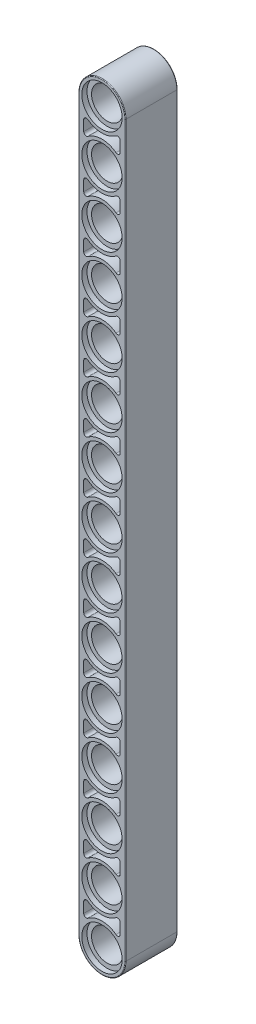
SolidWorks part; units mm, degrees
ref_plane "Front Plane" through (0, 0, 0) normal (0, 0, 1) x (1, 0, 0)
ref_plane "Top Plane" through (0, 0, 0) normal (0, 1, 0) x (1, 0, 0)
ref_plane "Right Plane" through (0, 0, 0) normal (1, 0, 0) x (0, 0, -1)
ref_plane "Plane1" through (0, 0, 4) normal (0, 0, 1) x (1, 0, 0)
sketch "Sketch1" plane through (0, 0, 4) normal (0, 0, 1) x (1, 0, 0)
  line L0 (3.6, -56) -> (3.6, 56)
  line L1 (-3.6, 56) -> (-3.6, -56)
  line L2 (3.6, 0) -> (-3.6, 0) construction
  arc A0 (3.6, 56) -> (-3.6, 56) centre (0, 56) ccw
  arc A1 (-3.6, -56) -> (3.6, -56) centre (0, -56) ccw
  point P6 (0, 0)
  dimension "D2" = 3.6
  dimension "D1" = 112
extrude "Boss-Extrude1" add sketch "Sketch1" against normal blind 8
sketch "Sketch2" plane through (0, 0, 4) normal (0, 0, 1) x (1, 0, 0)
  line L0 (-2.8, -27.2) -> (-2.8, -28.8)
  line L1 (2.8, -28.8) -> (2.8, -27.2)
  arc A0 (2.16, -26.88) -> (-2.16, -26.88) centre (0, -24) cw
  arc A1 (-2.16, -26.88) -> (-2.8, -27.2) centre (-2.4, -27.2) ccw
  arc A2 (-2.8, -28.8) -> (-2.16, -29.12) centre (-2.4, -28.8) ccw
  arc A3 (-2.16, -29.12) -> (2.16, -29.12) centre (0, -32) cw
  arc A4 (2.16, -29.12) -> (2.8, -28.8) centre (2.4, -28.8) ccw
  arc A5 (2.8, -27.2) -> (2.16, -26.88) centre (2.4, -27.2) ccw
extrude "Cut-Extrude1" cut sketch "Sketch2" against normal blind 3.1
sketch "Sketch3" plane through (0, 0, 4) normal (0, 0, 1) x (1, 0, 0)
  line L0 (-2.8, -11.2) -> (-2.8, -12.8)
  line L1 (2.8, -12.8) -> (2.8, -11.2)
  arc A0 (2.16, -10.88) -> (-2.16, -10.88) centre (0, -8) cw
  arc A1 (-2.16, -10.88) -> (-2.8, -11.2) centre (-2.4, -11.2) ccw
  arc A2 (-2.8, -12.8) -> (-2.16, -13.12) centre (-2.4, -12.8) ccw
  arc A3 (-2.16, -13.12) -> (2.16, -13.12) centre (0, -16) cw
  arc A4 (2.16, -13.12) -> (2.8, -12.8) centre (2.4, -12.8) ccw
  arc A5 (2.8, -11.2) -> (2.16, -10.88) centre (2.4, -11.2) ccw
extrude "Cut-Extrude2" cut sketch "Sketch3" against normal blind 3.1
sketch "Sketch4" plane through (0, 0, 4) normal (0, 0, 1) x (1, 0, 0)
  line L0 (-2.8, 4.8) -> (-2.8, 3.2)
  line L1 (2.8, 3.2) -> (2.8, 4.8)
  arc A0 (2.16, 5.12) -> (-2.16, 5.12) centre (0, 8) cw
  arc A1 (-2.16, 5.12) -> (-2.8, 4.8) centre (-2.4, 4.8) ccw
  arc A2 (-2.8, 3.2) -> (-2.16, 2.88) centre (-2.4, 3.2) ccw
  arc A3 (-2.16, 2.88) -> (2.16, 2.88) centre (0, 0) cw
  arc A4 (2.16, 2.88) -> (2.8, 3.2) centre (2.4, 3.2) ccw
  arc A5 (2.8, 4.8) -> (2.16, 5.12) centre (2.4, 4.8) ccw
extrude "Cut-Extrude3" cut sketch "Sketch4" against normal blind 3.1
sketch "Sketch5" plane through (0, 0, 4) normal (0, 0, 1) x (1, 0, 0)
  line L0 (-2.8, 20.8) -> (-2.8, 19.2)
  line L1 (2.8, 19.2) -> (2.8, 20.8)
  arc A0 (2.16, 21.12) -> (-2.16, 21.12) centre (0, 24) cw
  arc A1 (-2.16, 21.12) -> (-2.8, 20.8) centre (-2.4, 20.8) ccw
  arc A2 (-2.8, 19.2) -> (-2.16, 18.88) centre (-2.4, 19.2) ccw
  arc A3 (-2.16, 18.88) -> (2.16, 18.88) centre (0, 16) cw
  arc A4 (2.16, 18.88) -> (2.8, 19.2) centre (2.4, 19.2) ccw
  arc A5 (2.8, 20.8) -> (2.16, 21.12) centre (2.4, 20.8) ccw
extrude "Cut-Extrude4" cut sketch "Sketch5" against normal blind 3.1
sketch "Sketch6" plane through (0, 0, 4) normal (0, 0, 1) x (1, 0, 0)
  line L0 (2.8, 27.2) -> (2.8, 28.8)
  line L1 (-2.8, 28.8) -> (-2.8, 27.2)
  arc A0 (2.8, 28.8) -> (2.16, 29.12) centre (2.4, 28.8) ccw
  arc A1 (2.16, 29.12) -> (-2.16, 29.12) centre (0, 32) cw
  arc A2 (-2.16, 29.12) -> (-2.8, 28.8) centre (-2.4, 28.8) ccw
  arc A3 (-2.8, 27.2) -> (-2.16, 26.88) centre (-2.4, 27.2) ccw
  arc A4 (-2.16, 26.88) -> (2.16, 26.88) centre (0, 24) cw
  arc A5 (2.16, 26.88) -> (2.8, 27.2) centre (2.4, 27.2) ccw
extrude "Cut-Extrude5" cut sketch "Sketch6" against normal blind 3.1
sketch "Sketch7" plane through (0, 0, 4) normal (0, 0, 1) x (1, 0, 0)
  line L0 (-2.8, 12.8) -> (-2.8, 11.2)
  line L1 (2.8, 11.2) -> (2.8, 12.8)
  arc A0 (2.16, 13.12) -> (-2.16, 13.12) centre (0, 16) cw
  arc A1 (-2.16, 13.12) -> (-2.8, 12.8) centre (-2.4, 12.8) ccw
  arc A2 (-2.8, 11.2) -> (-2.16, 10.88) centre (-2.4, 11.2) ccw
  arc A3 (-2.16, 10.88) -> (2.16, 10.88) centre (0, 8) cw
  arc A4 (2.16, 10.88) -> (2.8, 11.2) centre (2.4, 11.2) ccw
  arc A5 (2.8, 12.8) -> (2.16, 13.12) centre (2.4, 12.8) ccw
extrude "Cut-Extrude6" cut sketch "Sketch7" against normal blind 3.1
sketch "Sketch8" plane through (0, 0, 4) normal (0, 0, 1) x (1, 0, 0)
  line L0 (-2.8, -3.2) -> (-2.8, -4.8)
  line L1 (2.8, -4.8) -> (2.8, -3.2)
  arc A0 (2.16, -2.88) -> (-2.16, -2.88) centre (0, 0) cw
  arc A1 (-2.16, -2.88) -> (-2.8, -3.2) centre (-2.4, -3.2) ccw
  arc A2 (-2.8, -4.8) -> (-2.16, -5.12) centre (-2.4, -4.8) ccw
  arc A3 (-2.16, -5.12) -> (2.16, -5.12) centre (0, -8) cw
  arc A4 (2.16, -5.12) -> (2.8, -4.8) centre (2.4, -4.8) ccw
  arc A5 (2.8, -3.2) -> (2.16, -2.88) centre (2.4, -3.2) ccw
extrude "Cut-Extrude7" cut sketch "Sketch8" against normal blind 3.1
sketch "Sketch9" plane through (0, 0, 4) normal (0, 0, 1) x (1, 0, 0)
  line L0 (-2.8, -19.2) -> (-2.8, -20.8)
  line L1 (2.8, -20.8) -> (2.8, -19.2)
  arc A0 (2.16, -18.88) -> (-2.16, -18.88) centre (0, -16) cw
  arc A1 (-2.16, -18.88) -> (-2.8, -19.2) centre (-2.4, -19.2) ccw
  arc A2 (-2.8, -20.8) -> (-2.16, -21.12) centre (-2.4, -20.8) ccw
  arc A3 (-2.16, -21.12) -> (2.16, -21.12) centre (0, -24) cw
  arc A4 (2.16, -21.12) -> (2.8, -20.8) centre (2.4, -20.8) ccw
  arc A5 (2.8, -19.2) -> (2.16, -18.88) centre (2.4, -19.2) ccw
extrude "Cut-Extrude8" cut sketch "Sketch9" against normal blind 3.1
sketch "Sketch10" plane through (0, 0, -4) normal (0, 0, -1) x (-1, 0, 0)
  line L0 (-2.8, -27.2) -> (-2.8, -28.8)
  line L1 (2.8, -28.8) -> (2.8, -27.2)
  arc A0 (-2.8, -28.8) -> (-2.16, -29.12) centre (-2.4, -28.8) ccw
  arc A1 (-2.16, -29.12) -> (2.16, -29.12) centre (0, -32) cw
  arc A2 (2.16, -29.12) -> (2.8, -28.8) centre (2.4, -28.8) ccw
  arc A3 (2.8, -27.2) -> (2.16, -26.88) centre (2.4, -27.2) ccw
  arc A4 (2.16, -26.88) -> (-2.16, -26.88) centre (0, -24) cw
  arc A5 (-2.16, -26.88) -> (-2.8, -27.2) centre (-2.4, -27.2) ccw
extrude "Cut-Extrude9" cut sketch "Sketch10" against normal blind 3.1
sketch "Sketch11" plane through (0, 0, -4) normal (0, 0, -1) x (-1, 0, 0)
  line L0 (-2.8, -19.2) -> (-2.8, -20.8)
  line L1 (2.8, -20.8) -> (2.8, -19.2)
  arc A0 (-2.8, -20.8) -> (-2.16, -21.12) centre (-2.4, -20.8) ccw
  arc A1 (-2.16, -21.12) -> (2.16, -21.12) centre (0, -24) cw
  arc A2 (2.16, -21.12) -> (2.8, -20.8) centre (2.4, -20.8) ccw
  arc A3 (2.8, -19.2) -> (2.16, -18.88) centre (2.4, -19.2) ccw
  arc A4 (2.16, -18.88) -> (-2.16, -18.88) centre (0, -16) cw
  arc A5 (-2.16, -18.88) -> (-2.8, -19.2) centre (-2.4, -19.2) ccw
extrude "Cut-Extrude10" cut sketch "Sketch11" against normal blind 3.1
sketch "Sketch12" plane through (0, 0, -4) normal (0, 0, -1) x (-1, 0, 0)
  line L0 (-2.8, -11.2) -> (-2.8, -12.8)
  line L1 (2.8, -12.8) -> (2.8, -11.2)
  arc A0 (-2.8, -12.8) -> (-2.16, -13.12) centre (-2.4, -12.8) ccw
  arc A1 (-2.16, -13.12) -> (2.16, -13.12) centre (0, -16) cw
  arc A2 (2.16, -13.12) -> (2.8, -12.8) centre (2.4, -12.8) ccw
  arc A3 (2.8, -11.2) -> (2.16, -10.88) centre (2.4, -11.2) ccw
  arc A4 (2.16, -10.88) -> (-2.16, -10.88) centre (0, -8) cw
  arc A5 (-2.16, -10.88) -> (-2.8, -11.2) centre (-2.4, -11.2) ccw
extrude "Cut-Extrude11" cut sketch "Sketch12" against normal blind 3.1
sketch "Sketch13" plane through (0, 0, -4) normal (0, 0, -1) x (-1, 0, 0)
  line L0 (-2.8, -3.2) -> (-2.8, -4.8)
  line L1 (2.8, -4.8) -> (2.8, -3.2)
  arc A0 (-2.8, -4.8) -> (-2.16, -5.12) centre (-2.4, -4.8) ccw
  arc A1 (-2.16, -5.12) -> (2.16, -5.12) centre (0, -8) cw
  arc A2 (2.16, -5.12) -> (2.8, -4.8) centre (2.4, -4.8) ccw
  arc A3 (2.8, -3.2) -> (2.16, -2.88) centre (2.4, -3.2) ccw
  arc A4 (2.16, -2.88) -> (-2.16, -2.88) centre (0, 0) cw
  arc A5 (-2.16, -2.88) -> (-2.8, -3.2) centre (-2.4, -3.2) ccw
extrude "Cut-Extrude12" cut sketch "Sketch13" against normal blind 3.1
sketch "Sketch14" plane through (0, 0, -4) normal (0, 0, -1) x (-1, 0, 0)
  line L0 (-2.8, 4.8) -> (-2.8, 3.2)
  line L1 (2.8, 3.2) -> (2.8, 4.8)
  arc A0 (-2.8, 3.2) -> (-2.16, 2.88) centre (-2.4, 3.2) ccw
  arc A1 (-2.16, 2.88) -> (2.16, 2.88) centre (0, 0) cw
  arc A2 (2.16, 2.88) -> (2.8, 3.2) centre (2.4, 3.2) ccw
  arc A3 (2.8, 4.8) -> (2.16, 5.12) centre (2.4, 4.8) ccw
  arc A4 (2.16, 5.12) -> (-2.16, 5.12) centre (0, 8) cw
  arc A5 (-2.16, 5.12) -> (-2.8, 4.8) centre (-2.4, 4.8) ccw
extrude "Cut-Extrude13" cut sketch "Sketch14" against normal blind 3.1
sketch "Sketch15" plane through (0, 0, -4) normal (0, 0, -1) x (-1, 0, 0)
  line L0 (-2.8, 12.8) -> (-2.8, 11.2)
  line L1 (2.8, 11.2) -> (2.8, 12.8)
  arc A0 (-2.8, 11.2) -> (-2.16, 10.88) centre (-2.4, 11.2) ccw
  arc A1 (-2.16, 10.88) -> (2.16, 10.88) centre (0, 8) cw
  arc A2 (2.16, 10.88) -> (2.8, 11.2) centre (2.4, 11.2) ccw
  arc A3 (2.8, 12.8) -> (2.16, 13.12) centre (2.4, 12.8) ccw
  arc A4 (2.16, 13.12) -> (-2.16, 13.12) centre (0, 16) cw
  arc A5 (-2.16, 13.12) -> (-2.8, 12.8) centre (-2.4, 12.8) ccw
extrude "Cut-Extrude14" cut sketch "Sketch15" against normal blind 3.1
sketch "Sketch16" plane through (0, 0, -4) normal (0, 0, -1) x (-1, 0, 0)
  line L0 (-2.8, 20.8) -> (-2.8, 19.2)
  line L1 (2.8, 19.2) -> (2.8, 20.8)
  arc A0 (-2.8, 19.2) -> (-2.16, 18.88) centre (-2.4, 19.2) ccw
  arc A1 (-2.16, 18.88) -> (2.16, 18.88) centre (0, 16) cw
  arc A2 (2.16, 18.88) -> (2.8, 19.2) centre (2.4, 19.2) ccw
  arc A3 (2.8, 20.8) -> (2.16, 21.12) centre (2.4, 20.8) ccw
  arc A4 (2.16, 21.12) -> (-2.16, 21.12) centre (0, 24) cw
  arc A5 (-2.16, 21.12) -> (-2.8, 20.8) centre (-2.4, 20.8) ccw
extrude "Cut-Extrude15" cut sketch "Sketch16" against normal blind 3.1
sketch "Sketch17" plane through (0, 0, -4) normal (0, 0, -1) x (-1, 0, 0)
  line L0 (-2.8, 28.8) -> (-2.8, 27.2)
  line L1 (2.8, 27.2) -> (2.8, 28.8)
  arc A0 (-2.8, 27.2) -> (-2.16, 26.88) centre (-2.4, 27.2) ccw
  arc A1 (-2.16, 26.88) -> (2.16, 26.88) centre (0, 24) cw
  arc A2 (2.16, 26.88) -> (2.8, 27.2) centre (2.4, 27.2) ccw
  arc A3 (2.8, 28.8) -> (2.16, 29.12) centre (2.4, 28.8) ccw
  arc A4 (2.16, 29.12) -> (-2.16, 29.12) centre (0, 32) cw
  arc A5 (-2.16, 29.12) -> (-2.8, 28.8) centre (-2.4, 28.8) ccw
extrude "Cut-Extrude16" cut sketch "Sketch17" against normal blind 3.1
ref_plane "Plane2" through (0, -32, 0) normal (0, 1, 0) x (1, 0, 0)
sketch "Sketch18" plane through (0, -32, 0) normal (0, 1, 0) x (1, 0, 0)
  line L0 (3.1, 4) -> (0, 4)
  line L1 (0, 4) -> (0, -4)
  line L2 (0, -4) -> (3.1, -4)
  line L3 (3.1, -4) -> (3.1, -3.2)
  line L4 (3.1, -3.2) -> (2.4, -3.2)
  line L5 (2.4, -3.2) -> (2.4, 3.2)
  line L6 (2.4, 3.2) -> (3.1, 3.2)
  line L7 (3.1, 3.2) -> (3.1, 4)
  line L8 (0, 4) -> (0, -4) construction
revolve "Cut-Revolve1" cut sketch "Sketch18" angle 360 about L8
ref_plane "Plane3" through (0, -24, 0) normal (0, 1, 0) x (1, 0, 0)
sketch "Sketch19" plane through (0, -24, 0) normal (0, 1, 0) x (1, 0, 0)
  line L0 (3.1, 4) -> (0, 4)
  line L1 (0, 4) -> (0, -4)
  line L2 (0, -4) -> (3.1, -4)
  line L3 (3.1, -4) -> (3.1, -3.2)
  line L4 (3.1, -3.2) -> (2.4, -3.2)
  line L5 (2.4, -3.2) -> (2.4, 3.2)
  line L6 (2.4, 3.2) -> (3.1, 3.2)
  line L7 (3.1, 3.2) -> (3.1, 4)
  line L8 (0, 4) -> (0, -4) construction
revolve "Cut-Revolve2" cut sketch "Sketch19" angle 360 about L8
ref_plane "Plane4" through (0, -16, 0) normal (0, 1, 0) x (1, 0, 0)
sketch "Sketch20" plane through (0, -16, 0) normal (0, 1, 0) x (1, 0, 0)
  line L0 (3.1, 4) -> (0, 4)
  line L1 (0, 4) -> (0, -4)
  line L2 (0, -4) -> (3.1, -4)
  line L3 (3.1, -4) -> (3.1, -3.2)
  line L4 (3.1, -3.2) -> (2.4, -3.2)
  line L5 (2.4, -3.2) -> (2.4, 3.2)
  line L6 (2.4, 3.2) -> (3.1, 3.2)
  line L7 (3.1, 3.2) -> (3.1, 4)
  line L8 (0, 4) -> (0, -4) construction
revolve "Cut-Revolve3" cut sketch "Sketch20" angle 360 about L8
ref_plane "Plane5" through (0, -8, 0) normal (0, 1, 0) x (1, 0, 0)
sketch "Sketch21" plane through (0, -8, 0) normal (0, 1, 0) x (1, 0, 0)
  line L0 (3.1, 4) -> (0, 4)
  line L1 (0, 4) -> (0, -4)
  line L2 (0, -4) -> (3.1, -4)
  line L3 (3.1, -4) -> (3.1, -3.2)
  line L4 (3.1, -3.2) -> (2.4, -3.2)
  line L5 (2.4, -3.2) -> (2.4, 3.2)
  line L6 (2.4, 3.2) -> (3.1, 3.2)
  line L7 (3.1, 3.2) -> (3.1, 4)
  line L8 (0, 4) -> (0, -4) construction
revolve "Cut-Revolve4" cut sketch "Sketch21" angle 360 about L8
sketch "Sketch22" plane through (0, 0, 0) normal (0, 1, 0) x (1, 0, 0)
  line L0 (3.1, 4) -> (0, 4)
  line L1 (0, 4) -> (0, -4)
  line L2 (0, -4) -> (3.1, -4)
  line L3 (3.1, -4) -> (3.1, -3.2)
  line L4 (3.1, -3.2) -> (2.4, -3.2)
  line L5 (2.4, -3.2) -> (2.4, 3.2)
  line L6 (2.4, 3.2) -> (3.1, 3.2)
  line L7 (3.1, 3.2) -> (3.1, 4)
  line L8 (0, 4) -> (0, -4) construction
revolve "Cut-Revolve5" cut sketch "Sketch22" angle 360 about L8
ref_plane "Plane6" through (0, 8, 0) normal (0, 1, 0) x (1, 0, 0)
sketch "Sketch23" plane through (0, 8, 0) normal (0, 1, 0) x (1, 0, 0)
  line L0 (3.1, 4) -> (0, 4)
  line L1 (0, 4) -> (0, -4)
  line L2 (0, -4) -> (3.1, -4)
  line L3 (3.1, -4) -> (3.1, -3.2)
  line L4 (3.1, -3.2) -> (2.4, -3.2)
  line L5 (2.4, -3.2) -> (2.4, 3.2)
  line L6 (2.4, 3.2) -> (3.1, 3.2)
  line L7 (3.1, 3.2) -> (3.1, 4)
  line L8 (0, 4) -> (0, -4) construction
revolve "Cut-Revolve6" cut sketch "Sketch23" angle 360 about L8
ref_plane "Plane7" through (0, 16, 0) normal (0, 1, 0) x (1, 0, 0)
sketch "Sketch24" plane through (0, 16, 0) normal (0, 1, 0) x (1, 0, 0)
  line L0 (3.1, 4) -> (0, 4)
  line L1 (0, 4) -> (0, -4)
  line L2 (0, -4) -> (3.1, -4)
  line L3 (3.1, -4) -> (3.1, -3.2)
  line L4 (3.1, -3.2) -> (2.4, -3.2)
  line L5 (2.4, -3.2) -> (2.4, 3.2)
  line L6 (2.4, 3.2) -> (3.1, 3.2)
  line L7 (3.1, 3.2) -> (3.1, 4)
  line L8 (0, 4) -> (0, -4) construction
revolve "Cut-Revolve7" cut sketch "Sketch24" angle 360 about L8
ref_plane "Plane8" through (0, 24, 0) normal (0, 1, 0) x (1, 0, 0)
sketch "Sketch25" plane through (0, 24, 0) normal (0, 1, 0) x (1, 0, 0)
  line L0 (3.1, 4) -> (0, 4)
  line L1 (0, 4) -> (0, -4)
  line L2 (0, -4) -> (3.1, -4)
  line L3 (3.1, -4) -> (3.1, -3.2)
  line L4 (3.1, -3.2) -> (2.4, -3.2)
  line L5 (2.4, -3.2) -> (2.4, 3.2)
  line L6 (2.4, 3.2) -> (3.1, 3.2)
  line L7 (3.1, 3.2) -> (3.1, 4)
  line L8 (0, 4) -> (0, -4) construction
revolve "Cut-Revolve8" cut sketch "Sketch25" angle 360 about L8
ref_plane "Plane9" through (0, 32, 0) normal (0, 1, 0) x (1, 0, 0)
sketch "Sketch26" plane through (0, 32, 0) normal (0, 1, 0) x (1, 0, 0)
  line L0 (3.1, 4) -> (0, 4)
  line L1 (0, 4) -> (0, -4)
  line L2 (0, -4) -> (3.1, -4)
  line L3 (3.1, -4) -> (3.1, -3.2)
  line L4 (3.1, -3.2) -> (2.4, -3.2)
  line L5 (2.4, -3.2) -> (2.4, 3.2)
  line L6 (2.4, 3.2) -> (3.1, 3.2)
  line L7 (3.1, 3.2) -> (3.1, 4)
  line L8 (0, 4) -> (0, -4) construction
revolve "Cut-Revolve9" cut sketch "Sketch26" angle 360 about L8
fillet "Fillet1" radius 0.1 8 edges at (0, 59.6, -4) (3.6, 0, -4) (-3.6, 0, -4) (0, -59.6, -4) (-3.6, 0, 4) (0, 59.6, 4) (0, -59.6, 4) (3.6, 0, 4)
pattern_linear "LPattern1" count 4 spacing 8 along (0, 1, 0) count 12 spacing 8 along (0, -1, 0) of "Cut-Revolve9"
pattern_linear "LPattern2" count 9 spacing 8 along (0, -1, 0) count 6 spacing 8 along (0, 1, 0) of "Cut-Extrude6"
mirror "Mirror1" about plane through (0, 0, 0) normal (0, 0, 1) of "LPattern2"
sketch "Sketch27" plane through (0, 0, -4) normal (0, 0, -1) x (-1, 0, 0)
  line L0 (0, 0) -> (-3.6, 0)
  line L1 (-3.6, -56) -> (-3.6, 56) construction
